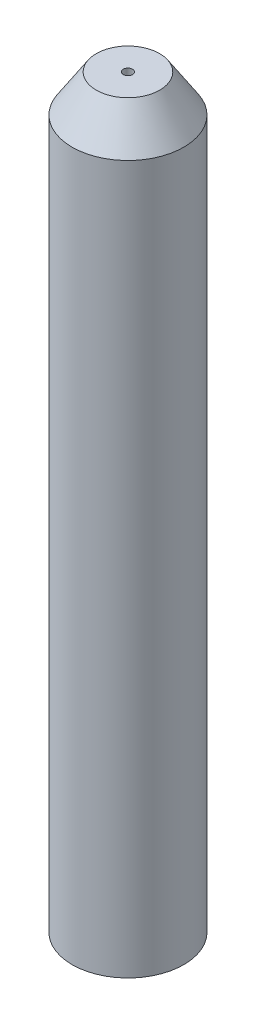
SolidWorks part; units mm, degrees
ref_plane "Front Plane" through (0, 0, 0) normal (0, 0, 1) x (1, 0, 0)
ref_plane "Top Plane" through (0, 0, 0) normal (0, 1, 0) x (1, 0, 0)
ref_plane "Right Plane" through (0, 0, 0) normal (1, 0, 0) x (0, 0, -1)
sketch "Sketch1" plane through (0, 0, 0) normal (0, 1, 0) x (1, 0, 0)
  circle A0 centre (0, 0) radius 3
  dimension "D1" = 6
extrude "Boss-Extrude1" add sketch "Sketch1" along normal blind 40
sketch "Sketch2" plane through (0, 40, 0) normal (0, 1, 0) x (1, 0, 0)
  circle A0 centre (0, 0) radius 0.25
  dimension "D1" = 0.5
extrude "Cut-Extrude1" cut sketch "Sketch2" against normal through all draft 3 draft outward yes
sketch "Sketch3" plane through (0, 40, 0) normal (0, 1, 0) x (1, 0, 0)
  circle A0 centre (0, 0) radius 2
  circle A1 centre (0, 0) radius 3
sketch "Sketch4" plane through (0, 40, 0) normal (0, 1, 0) x (1, 0, 0)
  circle A0 centre (0, 0) radius 0.25
  dimension "D1" = 0.5
extrude "Cut-Extrude3" cut sketch "Sketch4" against normal blind 20 draft 5 draft outward yes
chamfer "Chamfer2" distance 2 angle 33 1 edges at (0, 40, 3)
